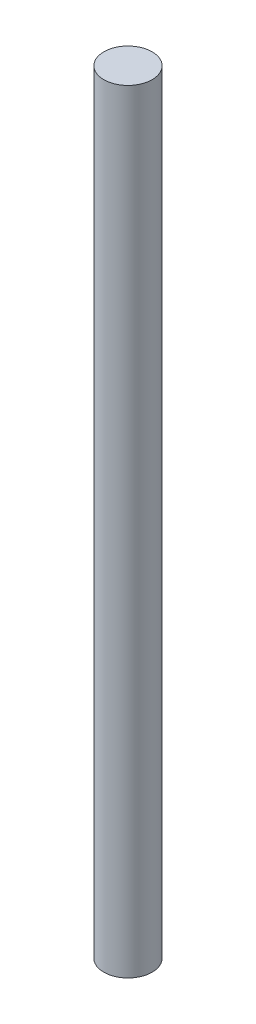
SolidWorks part; units mm, degrees
ref_plane "Front Plane" through (0, 0, 0) normal (0, 0, 1) x (1, 0, 0)
ref_plane "Top Plane" through (0, 0, 0) normal (0, 1, 0) x (1, 0, 0)
ref_plane "Right Plane" through (0, 0, 0) normal (1, 0, 0) x (0, 0, -1)
sketch "Sketch1" plane through (0, 0, 0) normal (0, 1, 0) x (1, 0, 0)
  circle A0 centre (0, 0) radius 3.175
  dimension "D1" = 6.35
extrude "Boss-Extrude1" add sketch "Sketch1" along normal blind 101.6
